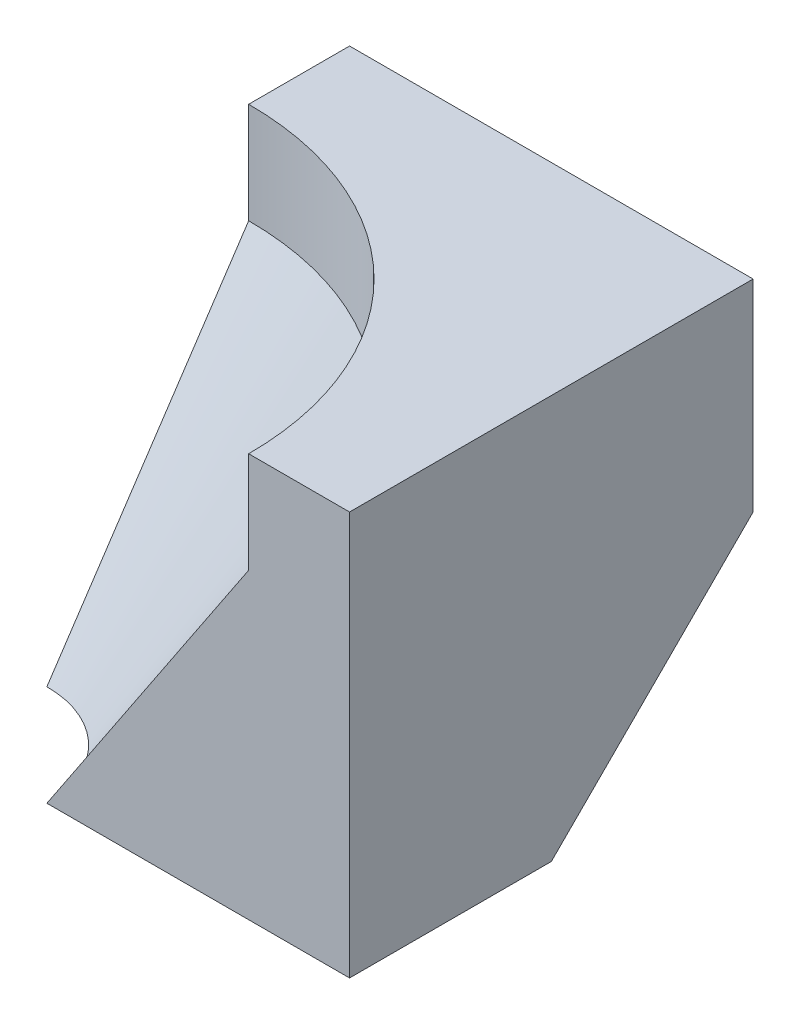
SolidWorks part; units mm, degrees
ref_plane "Front Plane" through (0, 0, 0) normal (0, 0, 1) x (1, 0, 0)
ref_plane "Top Plane" through (0, 0, 0) normal (0, 1, 0) x (1, 0, 0)
ref_plane "Right Plane" through (0, 0, 0) normal (1, 0, 0) x (0, 0, -1)
sketch "Sketch1" plane through (0, 0, 0) normal (0, 0, 1) x (1, 0, 0)
  line L1 (0, 0) -> (40, 0)
  line L2 (0, 0) -> (0, 40)
  line L3 (0, 40) -> (40, 40)
  line L4 (40, 0) -> (40, 40)
  dimension "D1" = 40
  dimension "D2" = 40
extrude "Boss-Extrude1" add sketch "Sketch1" along normal blind 40
sketch "Sketch2" plane through (0, 40, 0) normal (0, 1, 0) x (1, 0, 0)
  line L0 (40, -40) -> (0, -40) construction
  line L1 (0, -40) -> (0, 0) construction
  line L2 (0, -30) -> (0, -40)
  line L3 (0, -40) -> (10, -40)
  arc A0 (10, -40) -> (0, -30) centre (0, -40) ccw
  dimension "D1" = 10
extrude "Cut-Extrude1" cut sketch "Sketch2" against normal blind 40
sketch "Sketch3" plane through (40, 0, 0) normal (1, 0, 0) x (0, 0, -1)
  line L0 (0, 20) -> (-20, 0)
  line L1 (0, 0) -> (0, 40) construction
  line L2 (-40, 0) -> (0, 0) construction
  line L3 (-20, 0) -> (0, 0)
  line L4 (0, 0) -> (0, 20)
  dimension "D1" = 20
  dimension "D2" = 20
extrude "Cut-Extrude2" cut sketch "Sketch3" against normal blind 40
sketch "Sketch4" plane through (0, 40, 0) normal (0, 1, 0) x (1, 0, 0)
  line L0 (40, -40) -> (10, -40) construction
  line L1 (0, -30) -> (0, 0) construction
  line L2 (0, -10) -> (0, -30)
  line L3 (10, -40) -> (30, -40)
  arc A0 (30, -40) -> (0, -10) centre (0, -40) ccw
  arc A1 (0, -30) -> (10, -40) centre (0, -40) cw
  arc A2 (10, -40) -> (0, -30) centre (0, -40) ccw construction
  dimension "D1" = 30
extrude "Cut-Extrude3" cut sketch "Sketch4" against normal blind 10
ref_plane "Plane2" through (-12.2727, 8.1818, 12.2727) normal (0.6396, -0.4264, -0.6396) x (-0.7687, -0.3548, -0.5322)
ref_plane "Plane3" through (-13.3333, 6.6667, 13.3333) normal (0.6667, -0.3333, -0.6667) x (-0.7454, -0.2981, -0.5963)
sketch "Sketch8" plane through (-13.3333, 6.6667, 13.3333) normal (0.6667, -0.3333, -0.6667) x (-0.7454, -0.2981, -0.5963)
  line L0 (-17.8885, 31.305) -> (-17.8885, -13.4164)
  line L1 (-17.8885, -13.4164) -> (-31.305, -17.8885)
  line L2 (-31.305, -17.8885) -> (-58.1378, 17.8885)
  line L3 (-58.1378, 17.8885) -> (-17.8885, 31.305)
extrude "Boss-Extrude2" add sketch "Sketch8" along normal blind 28
sketch "Sketch19" plane through (0, 40, 0) normal (0, 1, 0) x (1, 0, 0)
  line L0 (40, -40) -> (30, -40) construction
  line L1 (0, -10) -> (0, -40)
  line L2 (0, -40) -> (30, -40)
  line L3 (30, -40) -> (29.6341, -40.1914)
  arc A0 (0, -10) -> (30, -40) centre (0, -40) cw
  arc M2 (0, -10) -> (30, -40) centre (0, -40) cw
extrude "Cut-Extrude11" cut sketch "Sketch19" against normal blind 10 contours L1 L2 M2
sketch "Sketch20" plane through (0, 0, 0) normal (0, 0, -1) x (-1, 0, 0)
  line L1 (0, 40) -> (-40, 40)
  line L2 (0, 40) -> (0, 20)
  line L3 (0, 20) -> (-40, 20)
  line L4 (-40, 40) -> (-40, 20)
extrude "Cut-Extrude12" cut sketch "Sketch20" along normal blind 10
sketch "Sketch21" plane through (0, 10, 10) normal (0, -0.7071, -0.7071) x (1, 0, 0)
  line L1 (0, -14.1421) -> (40, -14.1421)
  line L2 (0, -14.1421) -> (0, 14.1421)
  line L3 (0, 14.1421) -> (40, 14.1421)
  line L4 (40, -14.1421) -> (40, 14.1421)
extrude "Cut-Extrude13" cut sketch "Sketch21" along normal blind 10
sketch "Sketch22" plane through (0, 10, -10) normal (0, -0.7071, 0.7071) x (1, 0, 0)
  line L0 (16, 14.1421) -> (22, 14.1421)
  line L1 (22, 14.1421) -> (18.6667, 10.9994)
  line L2 (18.6667, 10.9994) -> (16, 14.1421)
extrude "Cut-Extrude14" cut sketch "Sketch22" against normal blind 10
sketch "Sketch23" plane through (0, 0, 0) normal (0, -1, 0) x (1, 0, 0)
  line L1 (40, 40) -> (0, 40)
  line L2 (40, 40) -> (40, 0)
  line L3 (40, 0) -> (0, 0)
  line L4 (0, 40) -> (0, 0)
  dimension "D1" = 40
  dimension "D2" = 40
extrude "Cut-Extrude15" cut sketch "Sketch23" along normal blind 10
sketch "Sketch24" plane through (40, 0, 0) normal (1, 0, 0) x (0, 0, -1)
  line L1 (-40, 0) -> (0, 0)
  line L2 (-40, 0) -> (-40, 40)
  line L3 (-40, 40) -> (0, 40)
  line L4 (0, 0) -> (0, 40)
extrude "Cut-Extrude16" cut sketch "Sketch24" along normal blind 10
ref_plane "Plane4" through (-12.2727, 8.1818, 12.2727) normal (-0.6396, 0.4264, 0.6396) x (0.7687, 0.3548, 0.5322)
sketch "Sketch25" plane through (-12.2727, 8.1818, 12.2727) normal (-0.6396, 0.4264, 0.6396) x (0.7687, 0.3548, 0.5322)
  line L0 (15.9654, -16.641) -> (15.9654, 19.4145)
  line L1 (15.9654, 19.4145) -> (54.9921, 2.7735)
  line L2 (54.9921, 2.7735) -> (28.9743, -22.188)
  line L3 (28.9743, -22.188) -> (15.9654, -16.641)
extrude "Cut-Extrude17" cut sketch "Sketch25" along normal blind 59
sketch "Sketch26" plane through (0, 30, 0) normal (0, 1, 0) x (1, 0, 0)
  line L1 (0, -30) -> (0, -40)
  line L2 (0, -40) -> (10, -40)
  arc A0 (10, -40) -> (0, -30) centre (0, -40) ccw
  dimension "D1" = 10
  dimension "D2" = 0
  dimension "D3" = 20
extrude "Cut-Extrude18" cut sketch "Sketch26" against normal blind 59
sketch "Sketch27" plane through (0, 0, 40) normal (0, 0, 1) x (1, 0, 0)
  line L0 (30, 30) -> (10, 0)
  line L1 (10, 0) -> (10, 30)
  line L2 (30, 30) -> (0, 30) construction
  line L3 (10, 30) -> (30, 30)
  line L4 (0, 0) -> (0, 14.113) construction
  line L5 (0, 30) -> (0, 0) construction
revolve "Cut-Revolve1" cut sketch "Sketch27" angle 360 about L4
